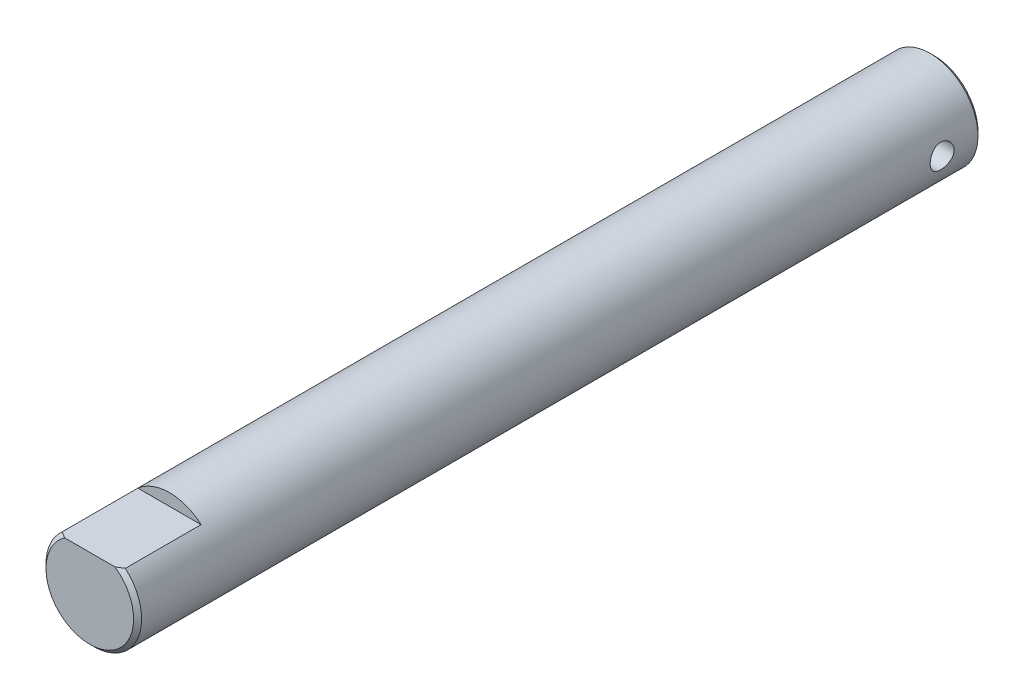
SolidWorks part; units mm, degrees
material "AISI 316 Annealed Stainless Steel Bar (SS)"
ref_plane "Front Plane" through (0, 0, 0) normal (0, 0, 1) x (1, 0, 0)
ref_plane "Top Plane" through (0, 0, 0) normal (0, 1, 0) x (1, 0, 0)
ref_plane "Right Plane" through (0, 0, 0) normal (1, 0, 0) x (0, 0, -1)
sketch "Sketch1" plane through (0, 0, 0) normal (0, 0, 1) x (1, 0, 0)
  circle A0 centre (0, 0) radius 6
  dimension "D1" = 12
extrude "Shaft" add sketch "Sketch1" along normal mid plane 106
sketch "Sketch2" plane through (0, 0, 0) normal (1, 0, 0) x (0, 0, -1)
  line L0 (53, -6) -> (53, 6) construction
  circle A0 centre (48, 0) radius 1.5
  dimension "D1" = 3
  dimension "D2" = 5
extrude "Hole" cut sketch "Sketch2" against normal up to next and the other way up to next
chamfer "0.5x45 Chamfers" distance 0.5 angle 45 2 edges at (6, 0, -53) (6, 0, 53)
sketch "Sketch4" plane through (0, 0, 53) normal (0, 0, 1) x (1, 0, 0)
  line L0 (-3.9686, 4.5) -> (3.9686, 4.5)
  circle A0 centre (0, 0) radius 6 construction
  arc A1 (3.9686, 4.5) -> (-3.9686, 4.5) centre (0, 0) ccw
  dimension "D1" = 4.5
extrude "Flat" cut sketch "Sketch4" against normal blind 10
